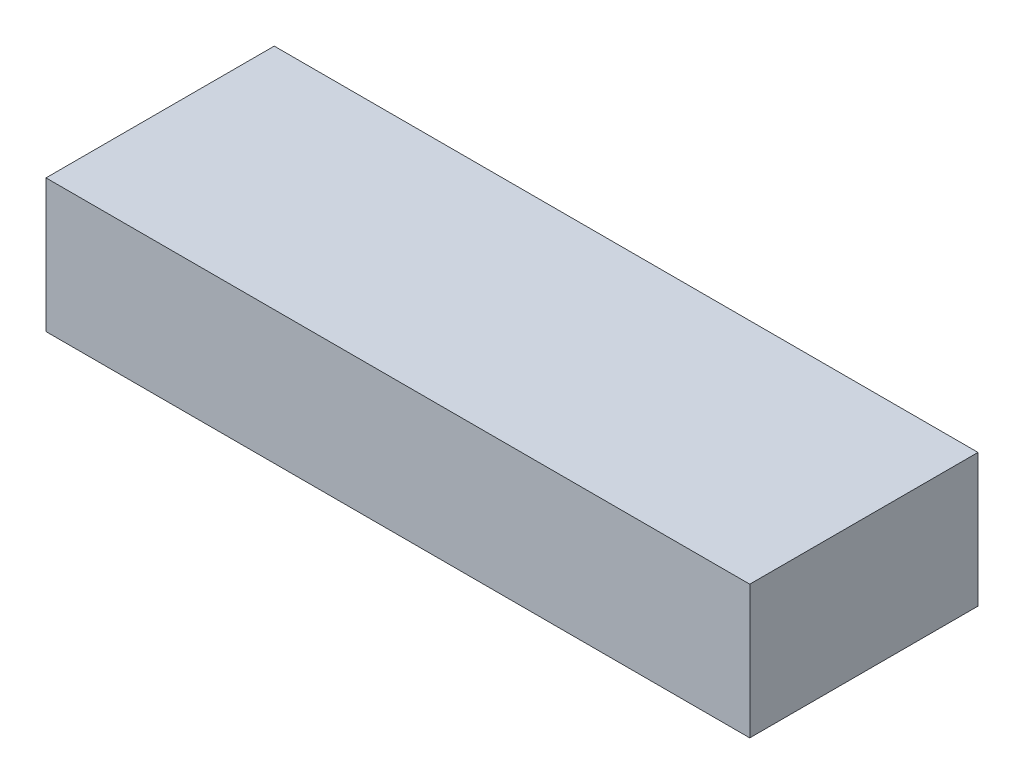
SolidWorks part; units mm, degrees
ref_plane "Front Plane" through (0, 0, 0) normal (0, 0, 1) x (1, 0, 0)
ref_plane "Top Plane" through (0, 0, 0) normal (0, 1, 0) x (1, 0, 0)
ref_plane "Right Plane" through (0, 0, 0) normal (1, 0, 0) x (0, 0, -1)
sketch "Sketch1" plane through (0, 0, 0) normal (0, 1, 0) x (1, 0, 0)
  line L1 (37, 12) -> (-37, 12)
  line L2 (37, 12) -> (37, -12)
  line L3 (37, -12) -> (-37, -12)
  line L4 (-37, 12) -> (-37, -12)
  line L5 (37, 12) -> (-37, -12) construction
  line L6 (37, -12) -> (-37, 12) construction
  point P0 (0, 0)
  dimension "D1" = 74
  dimension "D2" = 24
extrude "Boss-Extrude1" add sketch "Sketch1" along normal blind 14
